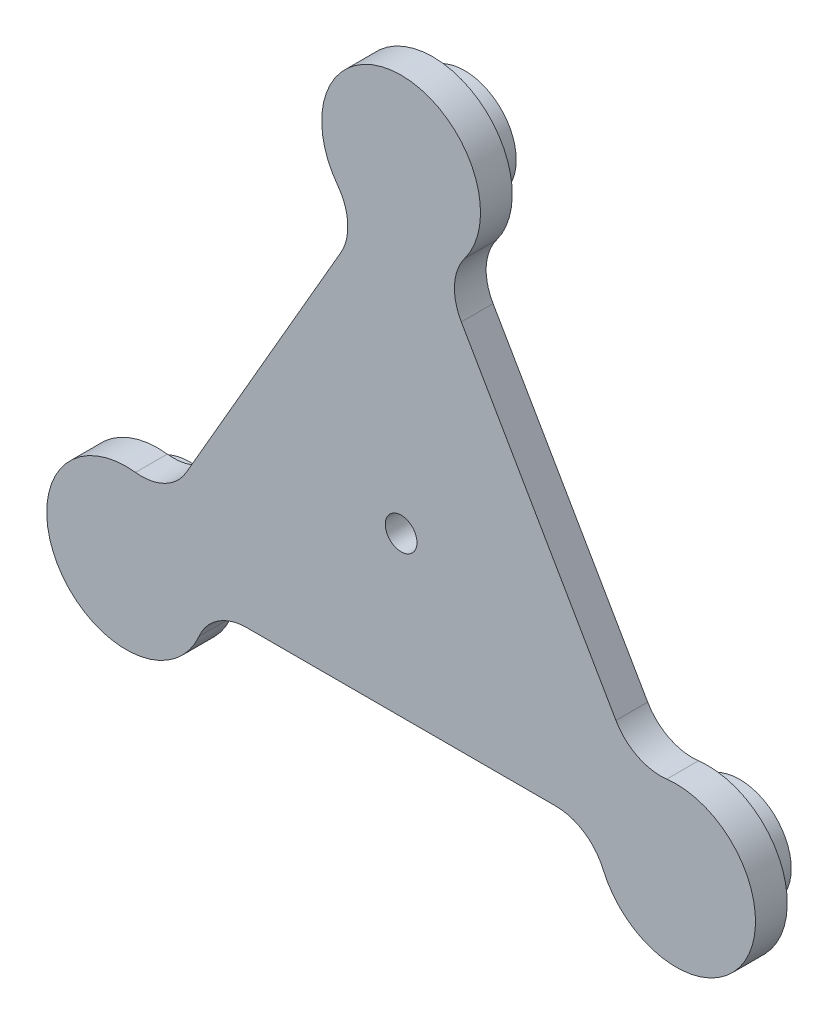
SolidWorks part; units mm, degrees
ref_plane "Front Plane" through (0, 0, 0) normal (0, 0, 1) x (1, 0, 0)
ref_plane "Top Plane" through (0, 0, 0) normal (0, 1, 0) x (1, 0, 0)
ref_plane "Right Plane" through (0, 0, 0) normal (1, 0, 0) x (0, 0, -1)
sketch "Sketch1" plane through (0, 0, 0) normal (0, 0, -1) x (1, 0, 0)
  line L0 (18.9572, -67.1651) -> (67.6453, 17.1652)
  line L1 (-67.6453, 17.1652) -> (-18.9572, -67.1652)
  line L6 (48.6881, 50) -> (-48.6881, 50)
  arc A1 (-63.6241, 59.8485) -> (-83.6423, 25.1758) centre (-86.6025, 50) ccw
  circle A3 centre (-86.6025, 50) radius 16.25 construction
  arc A4 (-63.6241, 59.8485) -> (-48.6881, 50) centre (-48.6881, 66.25) ccw
  arc A5 (-83.6423, 25.1758) -> (-67.6453, 17.1652) centre (-81.7182, 9.0402) cw
  arc A6 (83.6423, 25.1759) -> (63.6241, 59.8485) centre (86.6025, 50) ccw
  circle A7 centre (86.6025, 50) radius 16.25 construction
  arc A8 (83.6423, 25.1759) -> (67.6453, 17.1652) centre (81.7182, 9.0402) ccw
  arc A9 (63.6241, 59.8485) -> (48.6881, 50) centre (48.6881, 66.25) cw
  arc A10 (-20.0182, -85.0243) -> (20.0183, -85.0243) centre (0, -100) ccw
  circle A11 centre (0, -100) radius 16.25 construction
  arc A12 (-20.0182, -85.0243) -> (-18.9572, -67.1652) centre (-33.0301, -75.2902) ccw
  arc A13 (20.0183, -85.0243) -> (18.9572, -67.1651) centre (33.0301, -75.2901) cw
  point P31 (0, 0)
  dimension "D3" = 50
  dimension "D4" = 32.5
  dimension "D5" = 16.25
  dimension "D6" = 3
extrude "Boss-Extrude1" add sketch "Sketch1" along normal blind 10 contours A10 A13 L0 A8 A6 A9 L6 A4 A1 A5 L1 A12 | A7
sketch "Sketch2" plane through (0, 0, -10) normal (0, 0, -1) x (1, 0, 0)
  circle A6 centre (86.6025, 50) radius 16.25
  circle A33 centre (0, -100) radius 16.25
  circle A34 centre (-86.6025, 50) radius 16.25
  point P7 (0, 0)
  dimension "D2" = 32.5
  dimension "D1" = 86.6025
  dimension "D3" = 50
extrude "Boss-Extrude2" add sketch "Sketch2" along normal blind 10
sketch "Sketch3" plane through (0, 0, 0) normal (0, 0, 1) x (1, 0, 0)
  circle A9 centre (0, 0) radius 5
extrude "Cut-Extrude1" cut sketch "Sketch3" against normal blind 10
